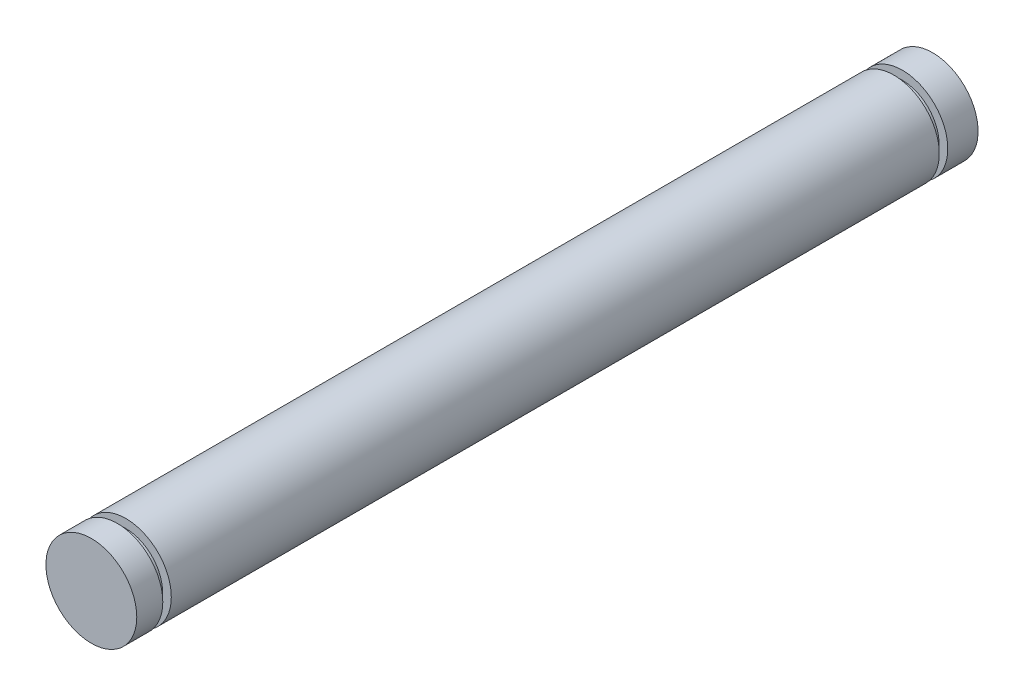
SolidWorks part; units mm, degrees
ref_plane "Front Plane" through (0, 0, 0) normal (0, 0, 1) x (1, 0, 0)
ref_plane "Top Plane" through (0, 0, 0) normal (0, 1, 0) x (1, 0, 0)
ref_plane "Right Plane" through (0, 0, 0) normal (1, 0, 0) x (0, 0, -1)
sketch "Sketch1" plane through (0, 0, 0) normal (0, 0, 1) x (1, 0, 0)
  circle A0 centre (0, 0) radius 4.7625
  dimension "D1" = 9.525
extrude "Boss-Extrude1" add sketch "Sketch1" along normal blind 97.3074
ref_plane "Plane1" through (0, 0, 7.2136) normal (0, 0, -1) x (-1, 0, 0)
sketch "Sketch3" plane through (0, 0, 7.2136) normal (0, 0, -1) x (-1, 0, 0)
  circle A0 centre (0, 0) radius 3.8481
  circle A1 centre (0, 0) radius 9.0789
  dimension "D1" = 7.6962
extrude "Cut-Extrude1" cut sketch "Sketch3" against normal mid plane 0.889
ref_plane "Plane2" through (0, 0, 88.6206) normal (0, 0, 1) x (1, 0, 0)
sketch "Sketch4" plane through (0, 0, 88.6206) normal (0, 0, 1) x (1, 0, 0)
  circle A0 centre (0, 0) radius 3.8481
  circle A1 centre (0, 0) radius 7.7665
  dimension "D1" = 7.6962
extrude "Cut-Extrude2" cut sketch "Sketch4" against normal mid plane 0.889
sketch "Sketch5" plane through (0, 0, 97.3074) normal (0, 0, 1) x (1, 0, 0)
  circle A0 centre (0, 0) radius 6.35
extrude "Cut-Extrude3" cut sketch "Sketch5" against normal offset from surface (5.5118 mm away) 3.175 up to plane "Plane2"
sketch "Sketch6" plane through (0, 0, 0) normal (0, 0, -1) x (-1, 0, 0)
  circle A0 centre (0, 0) radius 6.35
extrude "Cut-Extrude4" cut sketch "Sketch6" against normal offset from surface (3.5941 mm away) 3.175 up to face at (-3.8481, 0, 6.7691)
